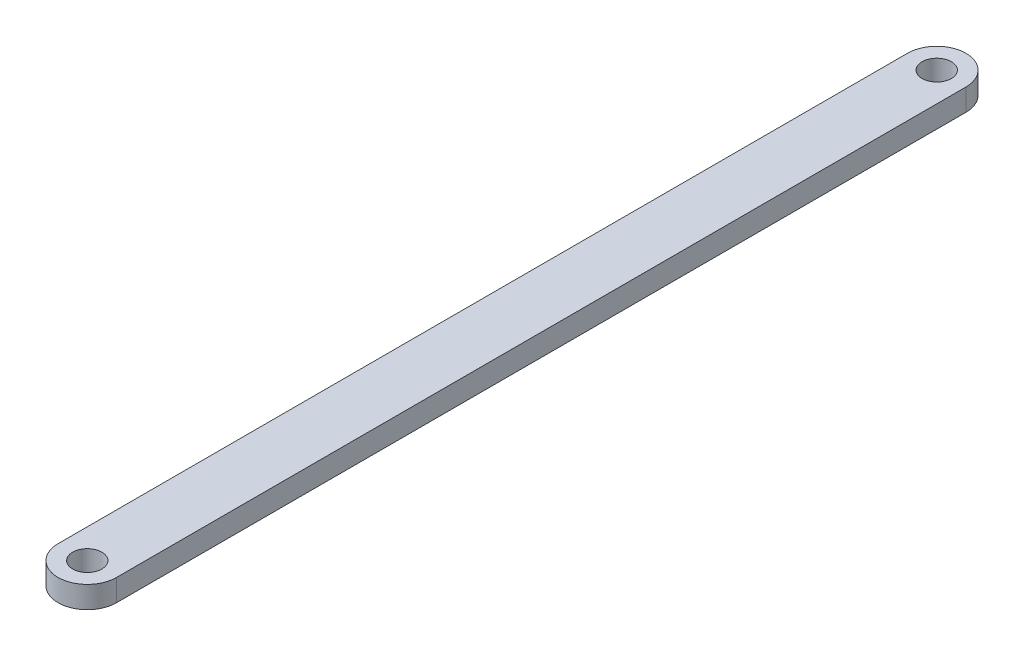
SolidWorks part; units mm, degrees
ref_plane "Front Plane" through (0, 0, 0) normal (0, 0, 1) x (1, 0, 0)
ref_plane "Top Plane" through (0, 0, 0) normal (0, 1, 0) x (1, 0, 0)
ref_plane "Right Plane" through (0, 0, 0) normal (1, 0, 0) x (0, 0, -1)
sketch "Sketch1" plane through (0, 0, 0) normal (0, 1, 0) x (1, 0, 0)
  line L0 (0, 58.125) -> (0, -58.125) construction
  line L1 (4, 58.125) -> (4, -58.125)
  line L2 (-4, 58.125) -> (-4, -58.125)
  arc A0 (4, 58.125) -> (-4, 58.125) centre (0, 58.125) ccw
  arc A1 (-4, -58.125) -> (4, -58.125) centre (0, -58.125) ccw
  circle A2 centre (0, 58.125) radius 2
  circle A3 centre (0, -58.125) radius 2
  point P2 (0, 0)
  dimension "D2" = 8
  dimension "D1" = 116.25
extrude "Boss-Extrude1" add sketch "Sketch1" along normal blind 3
